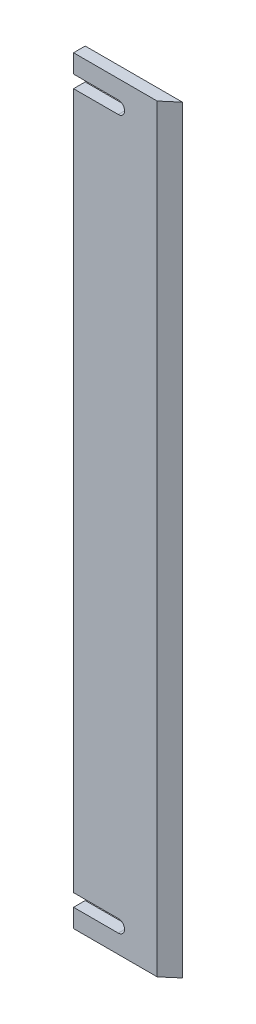
SolidWorks part; units mm, degrees
ref_plane "Alzado" through (0, 0, 0) normal (0, 0, 1) x (1, 0, 0)
ref_plane "Planta" through (0, 0, 0) normal (0, 1, 0) x (1, 0, 0)
ref_plane "Vista lateral" through (0, 0, 0) normal (1, 0, 0) x (0, 0, -1)
sketch "Sketch1" plane through (0, 0, 0) normal (0, 1, 0) x (1, 0, 0)
  line L0 (-12.8506, 0) -> (8.6494, 0)
  line L1 (8.6494, 0) -> (12.1494, 3)
  line L2 (12.1494, 3) -> (-12.8506, 3)
  line L3 (-12.8506, 3) -> (-12.8506, 0)
  dimension "D1" = 3
  dimension "D2" = 3.5
  dimension "D3" = 25
  dimension "D4" = 40.601
extrude "Boss-Extrude1" add sketch "Sketch1" along normal blind 195
sketch "Croquis1" plane through (0, 0, 0) normal (0, 0, 1) x (1, 0, 0)
  line L0 (-12.8506, 0) -> (8.6494, 0) construction
  line L1 (8.6494, 195) -> (8.6494, 0) construction
  line L2 (-1.3506, 4.75) -> (-12.8506, 4.75)
  line L3 (-12.8506, 195) -> (-12.8506, 0) construction
  line L4 (-12.8506, 4.75) -> (-12.8506, 8)
  line L5 (-12.8506, 8) -> (-1.3506, 8)
  line L6 (-12.8506, 97.5) -> (8.6494, 97.5) construction
  line L7 (-12.8506, 187) -> (-1.3506, 187)
  line L8 (-12.8506, 190.25) -> (-12.8506, 187)
  line L9 (-1.3506, 190.25) -> (-12.8506, 190.25)
  arc A0 (-1.3506, 4.75) -> (-1.3506, 8) centre (-1.3506, 6.375) ccw
  arc A1 (-1.3506, 190.25) -> (-1.3506, 187) centre (-1.3506, 188.625) cw
  dimension "D1" = 3.25
  dimension "D2" = 6.375
  dimension "D3" = 10
extrude "Cortar-Extruir4" cut sketch "Croquis1" against normal blind 10
